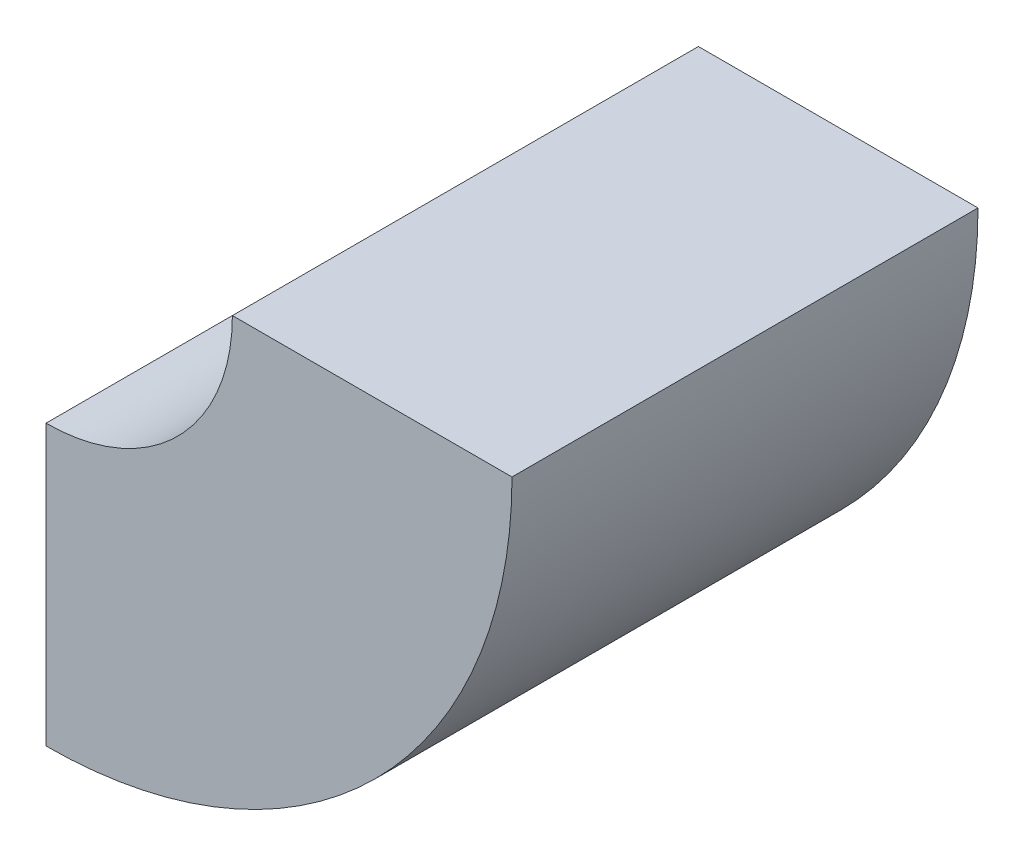
SolidWorks part; units mm, degrees
ref_plane "Front Plane" through (0, 0, 0) normal (0, 0, 1) x (1, 0, 0)
ref_plane "Top Plane" through (0, 0, 0) normal (0, 1, 0) x (1, 0, 0)
ref_plane "Right Plane" through (0, 0, 0) normal (1, 0, 0) x (0, 0, -1)
sketch "Sketch1" plane through (0, 0, 0) normal (0, 0, 1) x (1, 0, 0)
  line L0 (-15, 0) -> (0, 0)
  line L1 (-25, -10) -> (-25, -25)
  arc A0 (-25, -10) -> (-15, 0) centre (-25, 0) ccw
  arc A1 (-25, -25) -> (0, 0) centre (-25, 0) ccw
  dimension "D3" = 10
  dimension "D4" = 25
  dimension "D1" = 15
  dimension "D2" = 15
extrude "Boss-Extrude1" add sketch "Sketch1" along normal blind 25
